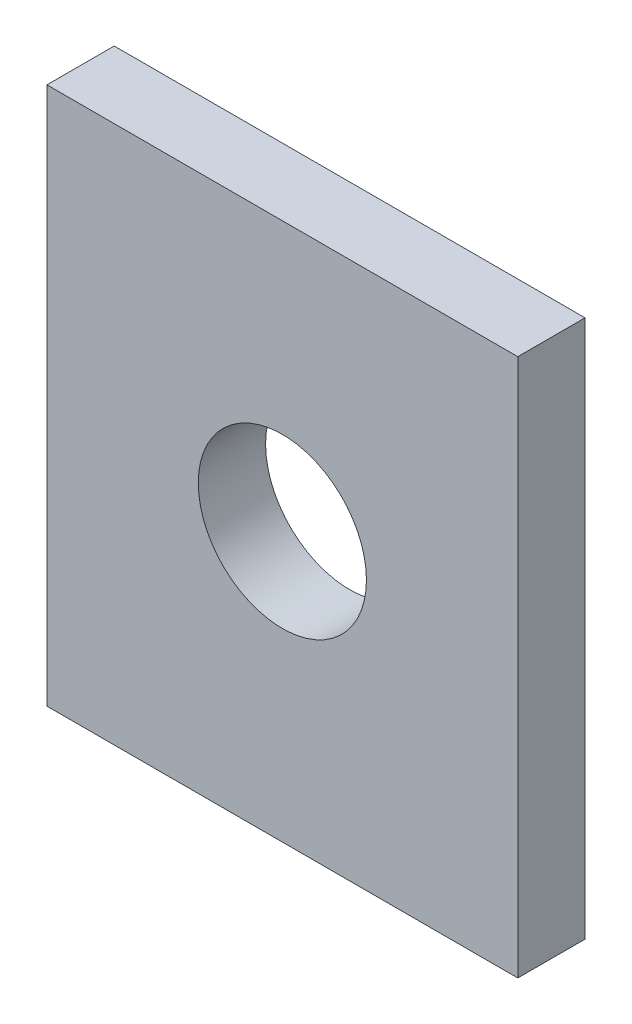
SolidWorks part; units mm, degrees
ref_plane "Front Plane" through (0, 0, 0) normal (0, 0, 1) x (1, 0, 0)
ref_plane "Top Plane" through (0, 0, 0) normal (0, 1, 0) x (1, 0, 0)
ref_plane "Right Plane" through (0, 0, 0) normal (1, 0, 0) x (0, 0, -1)
sketch "Sketch1" plane through (0, 0, 0) normal (0, 0, 1) x (1, 0, 0)
  line L1 (-17.5, -20) -> (17.5, -20)
  line L2 (-17.5, -20) -> (-17.5, 20)
  line L3 (-17.5, 20) -> (17.5, 20)
  line L4 (17.5, -20) -> (17.5, 20)
  line L5 (-17.5, -20) -> (17.5, 20) construction
  line L6 (-17.5, 20) -> (17.5, -20) construction
  point P0 (0, 0)
  dimension "D1" = 40
  dimension "D2" = 35
extrude "Boss-Extrude1" add sketch "Sketch1" along normal mid plane 5
sketch "Sketch2" plane through (0, 0, 2.5) normal (0, 0, 1) x (1, 0, 0)
  circle A0 centre (0, 0) radius 6.25
  dimension "D1" = 12.5
extrude "Cut-Extrude1" cut sketch "Sketch2" against normal through all
